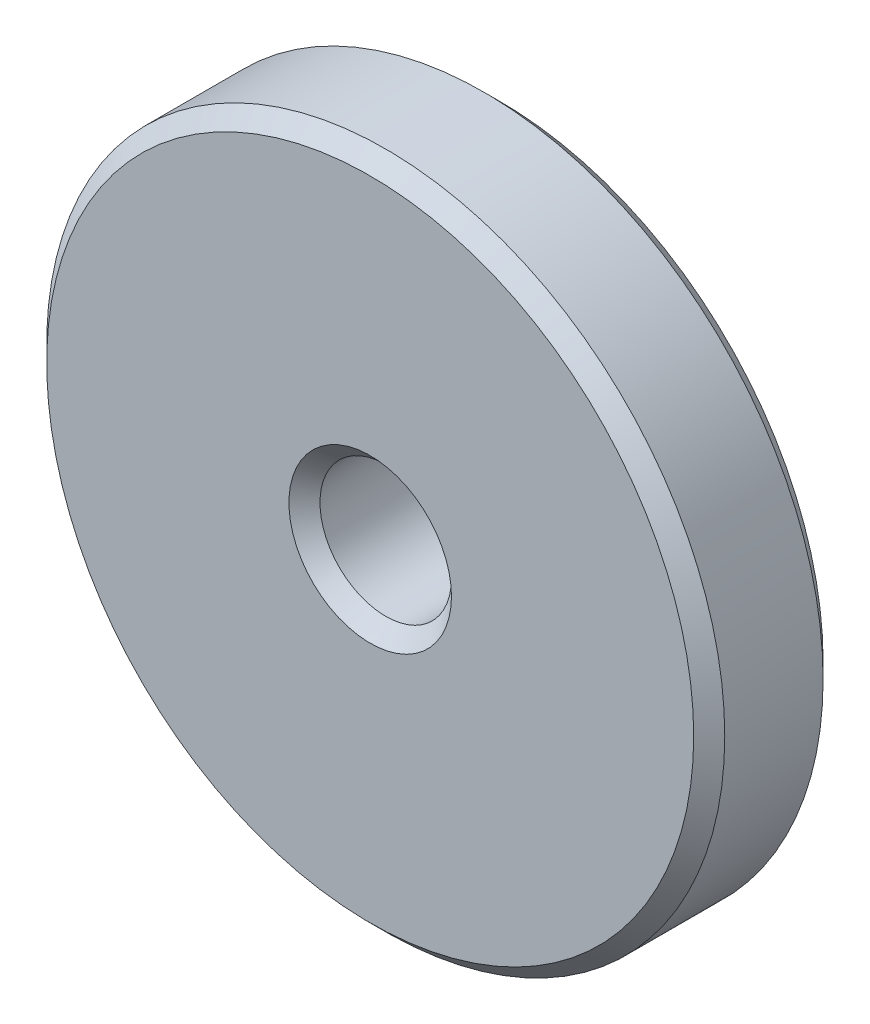
SolidWorks part; units mm, degrees
ref_plane "Front Plane" through (0, 0, 0) normal (0, 0, 1) x (1, 0, 0)
ref_plane "Top Plane" through (0, 0, 0) normal (0, 1, 0) x (1, 0, 0)
ref_plane "Right Plane" through (0, 0, 0) normal (1, 0, 0) x (0, 0, -1)
sketch "Sketch1" plane through (0, 0, 0) normal (0, 0, 1) x (1, 0, 0)
  circle A0 centre (0, 0) radius 12.7
  circle A1 centre (0, 0) radius 65.5
  dimension "D1" = 25.4
  dimension "D2" = 131
extrude "Boss-Extrude1" add sketch "Sketch1" along normal mid plane 25
chamfer "Chamfer1" distance 3 angle 45 4 edges at (12.7, 0, -12.5) (65.5, 0, -12.5) (12.7, 0, 12.5) (65.5, 0, 12.5)
